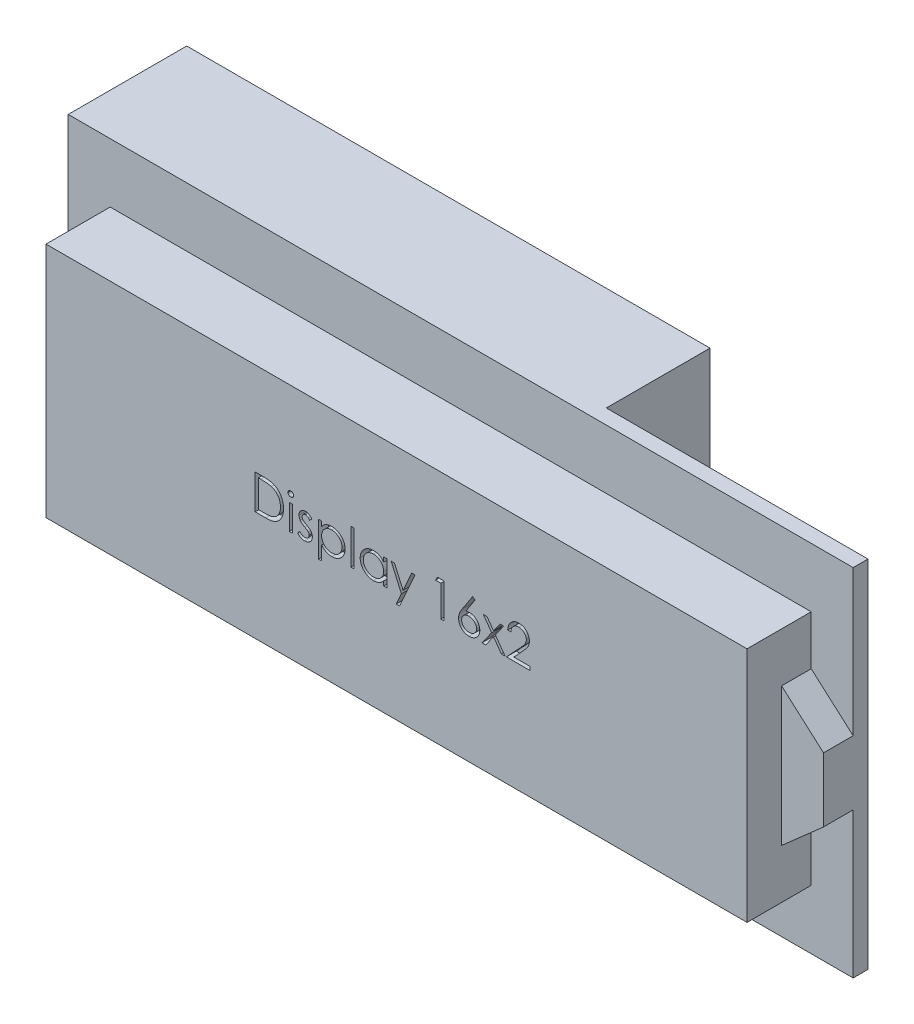
SolidWorks part; units mm, degrees
ref_plane "Plano frontal" through (0, 0, 0) normal (0, 0, 1) x (1, 0, 0)
ref_plane "Plano superior" through (0, 0, 0) normal (0, 1, 0) x (1, 0, 0)
ref_plane "Plano direito" through (0, 0, 0) normal (1, 0, 0) x (0, 0, -1)
sketch "Esboço1" plane through (0, 0, 0) normal (0, 0, 1) x (1, 0, 0)
  line L1 (-35.5, -12) -> (35.5, -12)
  line L2 (-35.5, -12) -> (-35.5, 12)
  line L3 (-35.5, 12) -> (35.5, 12)
  line L4 (35.5, -12) -> (35.5, 12)
  line L5 (-35.5, -12) -> (35.5, 12) construction
  line L6 (-35.5, 12) -> (35.5, -12) construction
  point P0 (0, 0)
extrude "Ressalto-extrusão1" add sketch "Esboço1" along normal blind 6.5
sketch "Esboço2" plane through (0, 0, 0) normal (0, 0, -1) x (-1, 0, 0)
  line L1 (-39.75, -18) -> (39.75, -18)
  line L2 (-39.75, -18) -> (-39.75, 18)
  line L3 (-39.75, 18) -> (39.75, 18)
  line L4 (39.75, -18) -> (39.75, 18)
  line L5 (-39.75, -18) -> (39.75, 18) construction
  line L6 (-39.75, 18) -> (39.75, -18) construction
  point P0 (0, 0)
extrude "Ressalto-extrusão2" add sketch "Esboço2" along normal blind 1.5
sketch "Esboço3" plane through (0, 0, 6.5) normal (0, 0, 1) x (1, 0, 0)
  line L1 (35.5, 12) -> (-35.5, 12) construction
  text T0 "Display 16x2"
other "Alinhar grupo1" parameters "D1"=12.8935
extrude "Corte-extrusão1" cut sketch "Esboço3" against normal blind 1
sketch "Esboço4" plane through (0, 0, -1.5) normal (0, 0, -1) x (-1, 0, 0)
  line L1 (-13.25, 18) -> (39.75, 18)
  line L2 (-13.25, 18) -> (-13.25, -0.5)
  line L3 (-13.25, -0.5) -> (39.75, -0.5)
  line L4 (39.75, 18) -> (39.75, -0.5)
  line L5 (-13.25, 18) -> (39.75, -0.5) construction
  line L6 (-13.25, -0.5) -> (39.75, 18) construction
  point P0 (13.25, 8.75)
  dimension "D1" = 53
  dimension "D2" = 18.5
extrude "Ressalto-extrusão3" add sketch "Esboço4" along normal blind 10.5
sketch "Esboço5" plane through (0, 0, 0) normal (0, 0, 1) x (1, 0, 0)
  line L0 (35.5, 7) -> (35.5, -7)
  line L1 (35.5, -12) -> (35.5, 12) construction
  line L2 (35.5, -7) -> (39.75, -3.25)
  line L3 (39.75, 18) -> (39.75, -18) construction
  line L4 (39.75, -3.25) -> (39.75, 3.25)
  line L5 (39.75, 3.25) -> (35.5, 7)
  point P4 (39.75, 0)
  point P9 (35.5, 0)
  dimension "D1" = 5
  dimension "D2" = 5
  dimension "D3" = 6.5
extrude "Ressalto-extrusão4" add sketch "Esboço5" along normal blind 3
